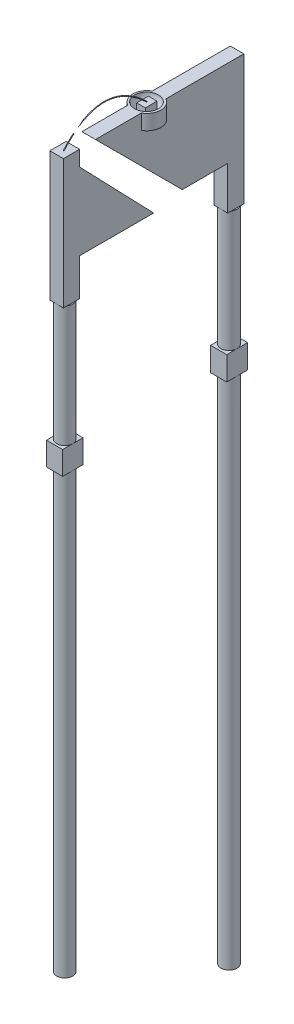
SolidWorks part; units mm, degrees
material "Cast Alloy Steel"
ref_plane "Front Plane" through (0, 0, 0) normal (0, 0, 1) x (1, 0, 0)
ref_plane "Top Plane" through (0, 0, 0) normal (0, 1, 0) x (1, 0, 0)
ref_plane "Right Plane" through (0, 0, 0) normal (1, 0, 0) x (0, 0, -1)
sketch "Sketch1" plane through (0, 0, 0) normal (1, 0, 0) x (0, 0, -1)
  line L0 (0, 0) -> (1.27, 0) construction
  line L1 (0, 0) -> (-1.27, 0) construction
  line L2 (-1.27, 0) -> (-1.27, -9)
  line L3 (1.27, 0) -> (1.27, -10)
  dimension "D1" = 1.27
  dimension "D2" = 1.27
  dimension "D3" = 10
  dimension "D4" = 9
sketch "Sketch8" plane through (0, 0, 0) normal (0, 1, 0) x (1, 0, 0)
  line L0 (0, 0) -> (0, -1.27) construction
  circle A0 centre (0, -1.27) radius 0.125
  dimension "D1" = 0.25
sweep "Sweep1" add profiles "Sketch8" path "Sketch1"
sketch "Sketch10" plane through (0, 0, 0) normal (0, 1, 0) x (1, 0, 0)
  line L0 (0, 0) -> (0, 1.27) construction
  circle A0 centre (0, 1.27) radius 0.125
  dimension "D1" = 0.25
extrude "Boss-Extrude2" add sketch "Sketch10" against normal blind 10.1643 separate body
sketch "Sketch11" plane through (0, 0, 0) normal (0, 1, 0) x (1, 0, 0)
  line L1 (-0.0965, -1.395) -> (0.0965, -1.395)
  line L2 (-0.0965, -1.395) -> (-0.0965, -1.145)
  line L3 (-0.0965, -1.145) -> (0.0965, -1.145)
  line L4 (0.0965, -1.395) -> (0.0965, -1.145)
  line L5 (-0.0965, -1.395) -> (0.0965, -1.145) construction
  line L6 (-0.0965, -1.145) -> (0.0965, -1.395) construction
  point P0 (0, -1.27)
sketch "Sketch12" plane through (0, 0, 0) normal (1, 0, 0) x (0, 0, -1)
  line L0 (-1.395, 0) -> (-1.395, 2)
  line L1 (-1.145, 0) -> (-1.145, 0.5737)
  line L2 (-1.395, 2) -> (-1.145, 2)
  line L3 (-1.145, 1.7623) -> (0, 0.5737)
  line L4 (0, 0.5737) -> (-1.145, 0.5737)
  line L5 (-1.145, 1.7623) -> (-1.145, 2)
  line L6 (-1.395, 0) -> (-1.145, 0)
  dimension "D1" = 2
extrude "Boss-Extrude4" add sketch "Sketch12" along normal blind 0.105 and the other way blind 0.105 contours L3 L4 L1 L6 L0 L2 L5
sketch "Sketch13" plane through (0, 0, 0) normal (1, 0, 0) x (0, 0, -1)
  line L0 (1.27, 0) -> (1.27, 2.0079) construction
  line L1 (1.145, 0) -> (1.145, 0.6659)
  line L2 (-0.8994, 2.0079) -> (0.4426, 0.6659)
  line L3 (0.4426, 0.6659) -> (1.145, 0.6659)
  line L4 (-0.8994, 2.0079) -> (1.27, 2.0079)
  line L5 (1.395, 0) -> (1.395, 2.0079)
  line L6 (1.395, 2.0079) -> (1.27, 2.0079)
  line L7 (1.145, 0) -> (1.395, 0)
extrude "Boss-Extrude5" add sketch "Sketch13" along normal blind 0.105 and the other way blind 0.105 contours L4 L6 L5 L7 L1 L3 L2
sketch "Sketch14" plane through (0, 2.0079, 0) normal (0, 1, 0) x (1, 0, 0)
  circle A0 centre (0, 0) radius 0.2163
sketch "Sketch15" plane through (0, 0, 0) normal (0, 0, 1) x (1, 0, 0)
  line L0 (0.2163, 2.0079) -> (-0.2163, 2.0079) construction
  line L1 (0.1788, 2.0079) -> (-0.1903, 2.0079)
  arc A0 (-0.1903, 2.0079) -> (0.1788, 2.0079) centre (-0.0057, 2.0079) ccw
extrude "Boss-Extrude6" add sketch "Sketch14" against normal blind 0.2329
revolve "Cut-Revolve8" cut sketch "Sketch15" angle 360 about L1
sketch "Sketch18" plane through (0, 2.0079, 0) normal (0, 1, 0) x (1, 0, 0)
  line L1 (0.0667, -0.0904) -> (-0.0667, -0.0904)
  line L2 (0.0667, -0.0904) -> (0.0667, 0.0904)
  line L3 (0.0667, 0.0904) -> (-0.0667, 0.0904)
  line L4 (-0.0667, -0.0904) -> (-0.0667, 0.0904)
  line L5 (0.0667, -0.0904) -> (-0.0667, 0.0904) construction
  line L6 (0.0667, 0.0904) -> (-0.0667, -0.0904) construction
  point P0 (0, 0)
extrude "Boss-Extrude7" add sketch "Sketch18" against normal blind 0.1248 separate body
sketch "Sketch19" plane through (0, 0, 0) normal (1, 0, 0) x (0, 0, -1)
  spline S0 degree 2 poles (0, 2.0129) (-0.6966, 2.6779) (-1.2945, 1.9887) knots 0 0 0 1 1 1
sweep "Sweep2" add path "Sketch19" circular profile diameter 0.01 parameters "D3"=0.01
sketch "Sketch44" plane through (0.105, 0, 0) normal (1, 0, 0) x (0, 0, -1)
  line L0 (0, 0) -> (0, -2.0499) construction
  line L1 (-2.4418, -2.0499) -> (2.4418, -2.0499)
  line L2 (-1.27, 0) -> (-1.27, -9) construction
  line L3 (-1.4276, -1.8699) -> (-1.1124, -1.8699)
  line L4 (-1.4276, -1.8699) -> (-1.4276, -2.2298)
  line L5 (-1.4276, -2.2298) -> (-1.1124, -2.2298)
  line L6 (-1.1124, -1.8699) -> (-1.1124, -2.2298)
  line L7 (-1.4276, -1.8699) -> (-1.1124, -2.2298) construction
  line L8 (-1.4276, -2.2298) -> (-1.1124, -1.8699) construction
  line L9 (1.1104, -1.8679) -> (1.4318, -1.8679)
  line L10 (1.1104, -1.8679) -> (1.1104, -2.2348)
  line L11 (1.1104, -2.2348) -> (1.4318, -2.2348)
  line L12 (1.4318, -1.8679) -> (1.4318, -2.2348)
  line L13 (1.1104, -1.8679) -> (1.4318, -2.2348) construction
  line L14 (1.1104, -2.2348) -> (1.4318, -1.8679) construction
  point P3 (-1.27, -2.0499)
  point P6 (0, -2.0499)
  point P13 (1.2711, -2.0514)
extrude "Boss-Extrude8" add sketch "Sketch44" against normal blind 0.23 and the other way blind 0.02 contours L6 L1 L4 L5 | L6 L3 L4 L1 | L12 L9 L10 L1 | L12 L1 L10 L11
